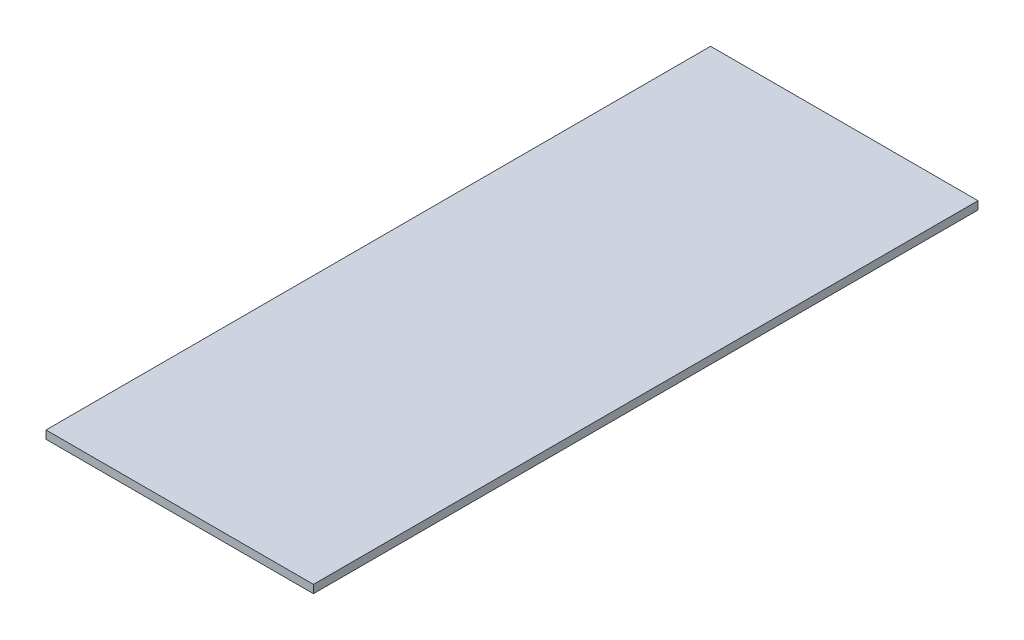
SolidWorks part; units mm, degrees
ref_plane "Front Plane" through (0, 0, 0) normal (0, 0, 1) x (1, 0, 0)
ref_plane "Top Plane" through (0, 0, 0) normal (0, 1, 0) x (1, 0, 0)
ref_plane "Right Plane" through (0, 0, 0) normal (1, 0, 0) x (0, 0, -1)
sketch "Sketch1" plane through (0, 0, 0) normal (0, 1, 0) x (1, 0, 0)
  line L0 (-33, -82) -> (-33, 82)
  line L1 (-23, -72) -> (23, -72) construction
  line L2 (-23, -72) -> (-23, 72) construction
  line L3 (-23, 72) -> (23, 72) construction
  line L4 (23, -72) -> (23, 72) construction
  line L5 (-23, -72) -> (23, 72) construction
  line L6 (-23, 72) -> (23, -72) construction
  line L7 (-33, 82) -> (33, 82)
  line L8 (33, -82) -> (33, 82)
  line L9 (-33, -82) -> (33, -82)
  point P0 (0, 0)
  dimension "D1" = 144
  dimension "D2" = 46
  dimension "D3" = 10
extrude "Boss-Extrude1" add sketch "Sketch1" along normal blind 2
